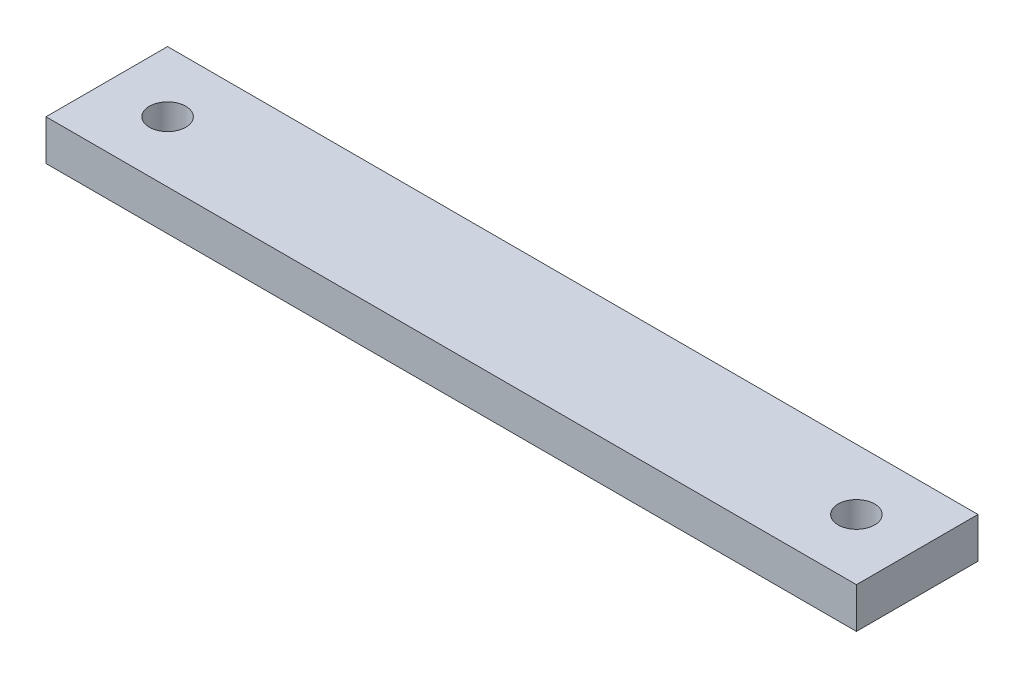
SolidWorks part; units mm, degrees
ref_plane "Front Plane" through (0, 0, 0) normal (0, 0, 1) x (1, 0, 0)
ref_plane "Top Plane" through (0, 0, 0) normal (0, 1, 0) x (1, 0, 0)
ref_plane "Right Plane" through (0, 0, 0) normal (1, 0, 0) x (0, 0, -1)
sketch "Sketch1" plane through (0, 0, 0) normal (0, 1, 0) x (1, 0, 0)
  line L36 (0, 0) -> (-200, 0)
  line L37 (-200, 0) -> (-200, 30)
  line L40 (-200, 30) -> (0, 30)
  line L43 (0, 30) -> (0, 0)
  circle A2 centre (-185, 15) radius 4.5
  circle A3 centre (-15, 15) radius 4.5
extrude "Boss-Extrude1" add sketch "Sketch1" along normal blind 10
